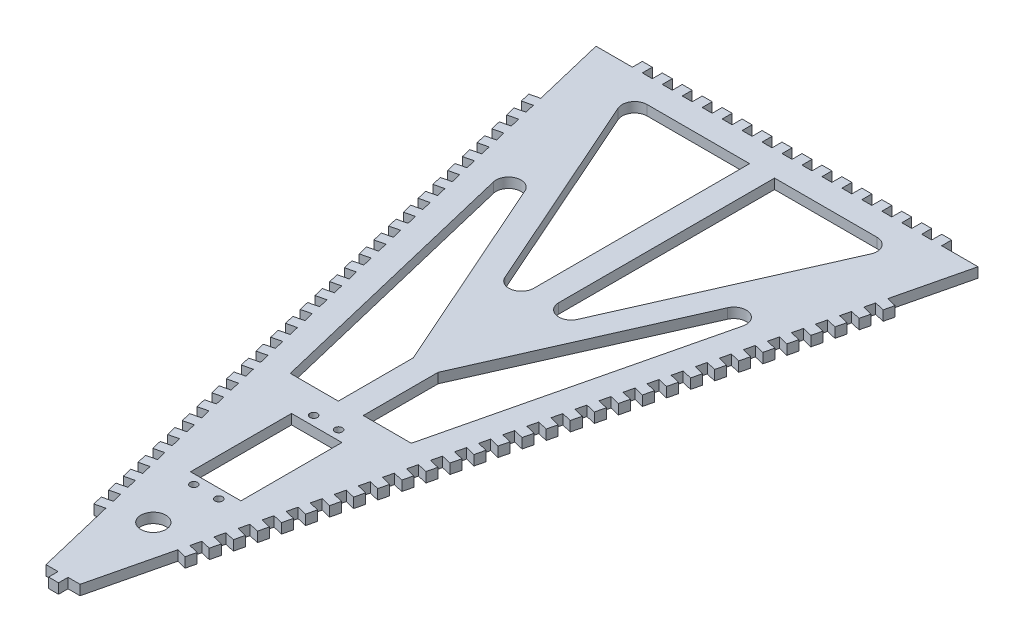
SolidWorks part; units mm, degrees
material "Cedar"
ref_plane "Front Plane" through (0, 0, 0) normal (0, 0, 1) x (1, 0, 0)
ref_plane "Top Plane" through (0, 0, 0) normal (0, 1, 0) x (1, 0, 0)
ref_plane "Right Plane" through (0, 0, 0) normal (1, 0, 0) x (0, 0, -1)
sketch "Sketch1" plane through (0, 0, 0) normal (0, 1, 0) x (1, 0, 0)
  line L0 (-76.56, 0) -> (76.56, 0)
  line L1 (76.56, 0) -> (6.83, -290.231)
  line L2 (6.83, -290.231) -> (-6.83, -290.231)
  line L3 (-6.83, -290.231) -> (-76.56, 0)
  line L4 (0, -290.231) -> (0, 0) construction
  dimension "D1" = 153.12
  dimension "D2" = 13.66
  dimension "D3" = 298.49
extrude "Boss-Extrude1" add sketch "Sketch1" against normal blind 4
sketch "Sketch2" plane through (0, 0, 0) normal (0, 1, 0) x (1, 0, 0)
  line L0 (0, 0) -> (0, -290.231) construction
  line L1 (-6.83, -290.231) -> (6.83, -290.231) construction
  line L2 (-69.5517, -29.1699) -> (-73.441, -30.1044)
  line L3 (-76.56, 0) -> (-6.83, -290.231) construction
  line L4 (-73.441, -30.1044) -> (-72.5066, -33.9937)
  line L5 (-72.5066, -33.9937) -> (-68.6173, -33.0592)
  line L6 (-68.6173, -33.0592) -> (-69.5517, -29.1699)
  line L7 (-67.6829, -36.9486) -> (-71.5722, -37.883)
  line L8 (-71.5722, -37.883) -> (-70.6377, -41.7723)
  line L9 (-70.6377, -41.7723) -> (-66.7484, -40.8379)
  line L10 (-66.7484, -40.8379) -> (-67.6829, -36.9486)
  line L11 (-65.814, -44.7272) -> (-69.7033, -45.6616)
  line L12 (-69.7033, -45.6616) -> (-68.7689, -49.551)
  line L13 (-68.7689, -49.551) -> (-64.8795, -48.6165)
  line L14 (-64.8795, -48.6165) -> (-65.814, -44.7272)
  line L15 (-63.9451, -52.5059) -> (-67.8344, -53.4403)
  line L16 (-67.8344, -53.4403) -> (-66.9, -57.3296)
  line L17 (-66.9, -57.3296) -> (-63.0107, -56.3952)
  line L18 (-63.0107, -56.3952) -> (-63.9451, -52.5059)
  line L19 (-62.0762, -60.2845) -> (-65.9656, -61.2189)
  line L20 (-65.9656, -61.2189) -> (-65.0311, -65.1083)
  line L21 (-65.0311, -65.1083) -> (-61.1418, -64.1738)
  line L22 (-61.1418, -64.1738) -> (-62.0762, -60.2845)
  line L23 (-60.2074, -68.0631) -> (-64.0967, -68.9976)
  line L24 (-64.0967, -68.9976) -> (-63.1622, -72.8869)
  line L25 (-63.1622, -72.8869) -> (-59.2729, -71.9525)
  line L26 (-59.2729, -71.9525) -> (-60.2074, -68.0631)
  line L27 (-58.3385, -75.8418) -> (-62.2278, -76.7762)
  line L28 (-62.2278, -76.7762) -> (-61.2934, -80.6655)
  line L29 (-61.2934, -80.6655) -> (-57.404, -79.7311)
  line L30 (-57.404, -79.7311) -> (-58.3385, -75.8418)
  line L31 (-56.4696, -83.6204) -> (-60.3589, -84.5549)
  line L32 (-60.3589, -84.5549) -> (-59.4245, -88.4442)
  line L33 (-59.4245, -88.4442) -> (-55.5352, -87.5098)
  line L34 (-55.5352, -87.5098) -> (-56.4696, -83.6204)
  line L35 (-54.6007, -91.3991) -> (-58.4901, -92.3335)
  line L36 (-58.4901, -92.3335) -> (-57.5556, -96.2228)
  line L37 (-57.5556, -96.2228) -> (-53.6663, -95.2884)
  line L38 (-53.6663, -95.2884) -> (-54.6007, -91.3991)
  line L39 (-52.7319, -99.1777) -> (-56.6212, -100.1122)
  line L40 (-56.6212, -100.1122) -> (-55.6868, -104.0015)
  line L41 (-55.6868, -104.0015) -> (-51.7974, -103.067)
  line L42 (-51.7974, -103.067) -> (-52.7319, -99.1777)
  line L43 (-50.863, -106.9564) -> (-54.7523, -107.8908)
  line L44 (-54.7523, -107.8908) -> (-53.8179, -111.7801)
  line L45 (-53.8179, -111.7801) -> (-49.9286, -110.8457)
  line L46 (-49.9286, -110.8457) -> (-50.863, -106.9564)
  line L47 (-48.9941, -114.735) -> (-52.8834, -115.6694)
  line L48 (-52.8834, -115.6694) -> (-51.949, -119.5588)
  line L49 (-51.949, -119.5588) -> (-48.0597, -118.6243)
  line L50 (-48.0597, -118.6243) -> (-48.9941, -114.735)
  line L51 (-47.1252, -122.5137) -> (-51.0146, -123.4481)
  line L52 (-51.0146, -123.4481) -> (-50.0801, -127.3374)
  line L53 (-50.0801, -127.3374) -> (-46.1908, -126.403)
  line L54 (-46.1908, -126.403) -> (-47.1252, -122.5137)
  line L55 (-45.2564, -130.2923) -> (-49.1457, -131.2267)
  line L56 (-49.1457, -131.2267) -> (-48.2113, -135.1161)
  line L57 (-48.2113, -135.1161) -> (-44.3219, -134.1816)
  line L58 (-44.3219, -134.1816) -> (-45.2564, -130.2923)
  line L59 (-43.3875, -138.0709) -> (-47.2768, -139.0054)
  line L60 (-47.2768, -139.0054) -> (-46.3424, -142.8947)
  line L61 (-46.3424, -142.8947) -> (-42.4531, -141.9603)
  line L62 (-42.4531, -141.9603) -> (-43.3875, -138.0709)
  line L63 (-41.5186, -145.8496) -> (-45.4079, -146.784)
  line L64 (-45.4079, -146.784) -> (-44.4735, -150.6733)
  line L65 (-44.4735, -150.6733) -> (-40.5842, -149.7389)
  line L66 (-40.5842, -149.7389) -> (-41.5186, -145.8496)
  line L67 (-39.6498, -153.6282) -> (-43.5391, -154.5627)
  line L68 (-43.5391, -154.5627) -> (-42.6046, -158.452)
  line L69 (-42.6046, -158.452) -> (-38.7153, -157.5176)
  line L70 (-38.7153, -157.5176) -> (-39.6498, -153.6282)
  line L71 (-37.7809, -161.4069) -> (-41.6702, -162.3413)
  line L72 (-41.6702, -162.3413) -> (-40.7358, -166.2306)
  line L73 (-40.7358, -166.2306) -> (-36.8464, -165.2962)
  line L74 (-36.8464, -165.2962) -> (-37.7809, -161.4069)
  line L75 (-35.912, -169.1855) -> (-39.8013, -170.12)
  line L76 (-39.8013, -170.12) -> (-38.8669, -174.0093)
  line L77 (-38.8669, -174.0093) -> (-34.9776, -173.0748)
  line L78 (-34.9776, -173.0748) -> (-35.912, -169.1855)
  line L79 (-34.0431, -176.9642) -> (-37.9325, -177.8986)
  line L80 (-37.9325, -177.8986) -> (-36.998, -181.7879)
  line L81 (-36.998, -181.7879) -> (-33.1087, -180.8535)
  line L82 (-33.1087, -180.8535) -> (-34.0431, -176.9642)
  line L83 (-32.1743, -184.7428) -> (-36.0636, -185.6772)
  line L84 (-36.0636, -185.6772) -> (-35.1291, -189.5666)
  line L85 (-35.1291, -189.5666) -> (-31.2398, -188.6321)
  line L86 (-31.2398, -188.6321) -> (-32.1743, -184.7428)
  line L87 (-30.3054, -192.5215) -> (-34.1947, -193.4559)
  line L88 (-34.1947, -193.4559) -> (-33.2603, -197.3452)
  line L89 (-33.2603, -197.3452) -> (-29.3709, -196.4108)
  line L90 (-29.3709, -196.4108) -> (-30.3054, -192.5215)
  line L91 (-28.4365, -200.3001) -> (-32.3258, -201.2345)
  line L92 (-32.3258, -201.2345) -> (-31.3914, -205.1239)
  line L93 (-31.3914, -205.1239) -> (-27.5021, -204.1894)
  line L94 (-27.5021, -204.1894) -> (-28.4365, -200.3001)
  line L95 (-26.5676, -208.0787) -> (-30.457, -209.0132)
  line L96 (-30.457, -209.0132) -> (-29.5225, -212.9025)
  line L97 (-29.5225, -212.9025) -> (-25.6332, -211.9681)
  line L98 (-25.6332, -211.9681) -> (-26.5676, -208.0787)
  line L99 (-24.6988, -215.8574) -> (-28.5881, -216.7918)
  line L100 (-28.5881, -216.7918) -> (-27.6537, -220.6811)
  line L101 (-27.6537, -220.6811) -> (-23.7643, -219.7467)
  line L102 (-23.7643, -219.7467) -> (-24.6988, -215.8574)
  line L103 (-22.8299, -223.636) -> (-26.7192, -224.5705)
  line L104 (-26.7192, -224.5705) -> (-25.7848, -228.4598)
  line L105 (-25.7848, -228.4598) -> (-21.8955, -227.5254)
  line L106 (-21.8955, -227.5254) -> (-22.8299, -223.636)
  line L107 (-20.961, -231.4147) -> (-24.8503, -232.3491)
  line L108 (-24.8503, -232.3491) -> (-23.9159, -236.2384)
  line L109 (-23.9159, -236.2384) -> (-20.0266, -235.304)
  line L110 (-20.0266, -235.304) -> (-20.961, -231.4147)
  line L111 (-19.0921, -239.1933) -> (-22.9815, -240.1278)
  line L112 (-22.9815, -240.1278) -> (-22.047, -244.0171)
  line L113 (-22.047, -244.0171) -> (-18.1577, -243.0826)
  line L114 (-18.1577, -243.0826) -> (-19.0921, -239.1933)
  line L115 (-17.2233, -246.972) -> (-21.1126, -247.9064)
  line L116 (-21.1126, -247.9064) -> (-20.1782, -251.7957)
  line L117 (-20.1782, -251.7957) -> (-16.2888, -250.8613)
  line L118 (-16.2888, -250.8613) -> (-17.2233, -246.972)
  line L119 (-15.3544, -254.7506) -> (-19.2437, -255.685)
  line L120 (-19.2437, -255.685) -> (-18.3093, -259.5744)
  line L121 (-18.3093, -259.5744) -> (-14.42, -258.6399)
  line L122 (-14.42, -258.6399) -> (-15.3544, -254.7506)
  line L123 (14.42, -258.6399) -> (15.3544, -254.7506)
  line L124 (18.3093, -259.5744) -> (14.42, -258.6399)
  line L125 (19.2437, -255.685) -> (18.3093, -259.5744)
  line L126 (15.3544, -254.7506) -> (19.2437, -255.685)
  line L127 (16.2888, -250.8613) -> (17.2233, -246.972)
  line L128 (20.1782, -251.7957) -> (16.2888, -250.8613)
  line L129 (21.1126, -247.9064) -> (20.1782, -251.7957)
  line L130 (17.2233, -246.972) -> (21.1126, -247.9064)
  line L131 (18.1577, -243.0826) -> (19.0921, -239.1933)
  line L132 (22.047, -244.0171) -> (18.1577, -243.0826)
  line L133 (22.9815, -240.1278) -> (22.047, -244.0171)
  line L134 (19.0921, -239.1933) -> (22.9815, -240.1278)
  line L135 (20.0266, -235.304) -> (20.961, -231.4147)
  line L136 (23.9159, -236.2384) -> (20.0266, -235.304)
  line L137 (24.8503, -232.3491) -> (23.9159, -236.2384)
  line L138 (20.961, -231.4147) -> (24.8503, -232.3491)
  line L139 (21.8955, -227.5254) -> (22.8299, -223.636)
  line L140 (25.7848, -228.4598) -> (21.8955, -227.5254)
  line L141 (26.7192, -224.5705) -> (25.7848, -228.4598)
  line L142 (22.8299, -223.636) -> (26.7192, -224.5705)
  line L143 (23.7643, -219.7467) -> (24.6988, -215.8574)
  line L144 (27.6537, -220.6811) -> (23.7643, -219.7467)
  line L145 (28.5881, -216.7918) -> (27.6537, -220.6811)
  line L146 (24.6988, -215.8574) -> (28.5881, -216.7918)
  line L147 (25.6332, -211.9681) -> (26.5676, -208.0787)
  line L148 (29.5225, -212.9025) -> (25.6332, -211.9681)
  line L149 (30.457, -209.0132) -> (29.5225, -212.9025)
  line L150 (26.5676, -208.0787) -> (30.457, -209.0132)
  line L151 (27.5021, -204.1894) -> (28.4365, -200.3001)
  line L152 (31.3914, -205.1239) -> (27.5021, -204.1894)
  line L153 (32.3258, -201.2345) -> (31.3914, -205.1239)
  line L154 (28.4365, -200.3001) -> (32.3258, -201.2345)
  line L155 (29.3709, -196.4108) -> (30.3054, -192.5215)
  line L156 (33.2603, -197.3452) -> (29.3709, -196.4108)
  line L157 (34.1947, -193.4559) -> (33.2603, -197.3452)
  line L158 (30.3054, -192.5215) -> (34.1947, -193.4559)
  line L159 (31.2398, -188.6321) -> (32.1743, -184.7428)
  line L160 (35.1291, -189.5666) -> (31.2398, -188.6321)
  line L161 (36.0636, -185.6772) -> (35.1291, -189.5666)
  line L162 (32.1743, -184.7428) -> (36.0636, -185.6772)
  line L163 (33.1087, -180.8535) -> (34.0431, -176.9642)
  line L164 (36.998, -181.7879) -> (33.1087, -180.8535)
  line L165 (37.9325, -177.8986) -> (36.998, -181.7879)
  line L166 (34.0431, -176.9642) -> (37.9325, -177.8986)
  line L167 (34.9776, -173.0748) -> (35.912, -169.1855)
  line L168 (38.8669, -174.0093) -> (34.9776, -173.0748)
  line L169 (39.8013, -170.12) -> (38.8669, -174.0093)
  line L170 (35.912, -169.1855) -> (39.8013, -170.12)
  line L171 (36.8464, -165.2962) -> (37.7809, -161.4069)
  line L172 (40.7358, -166.2306) -> (36.8464, -165.2962)
  line L173 (41.6702, -162.3413) -> (40.7358, -166.2306)
  line L174 (37.7809, -161.4069) -> (41.6702, -162.3413)
  line L175 (38.7153, -157.5176) -> (39.6498, -153.6282)
  line L176 (42.6046, -158.452) -> (38.7153, -157.5176)
  line L177 (43.5391, -154.5627) -> (42.6046, -158.452)
  line L178 (39.6498, -153.6282) -> (43.5391, -154.5627)
  line L179 (40.5842, -149.7389) -> (41.5186, -145.8496)
  line L180 (44.4735, -150.6733) -> (40.5842, -149.7389)
  line L181 (45.4079, -146.784) -> (44.4735, -150.6733)
  line L182 (41.5186, -145.8496) -> (45.4079, -146.784)
  line L183 (42.4531, -141.9603) -> (43.3875, -138.0709)
  line L184 (46.3424, -142.8947) -> (42.4531, -141.9603)
  line L185 (47.2768, -139.0054) -> (46.3424, -142.8947)
  line L186 (43.3875, -138.0709) -> (47.2768, -139.0054)
  line L187 (44.3219, -134.1816) -> (45.2564, -130.2923)
  line L188 (48.2113, -135.1161) -> (44.3219, -134.1816)
  line L189 (49.1457, -131.2267) -> (48.2113, -135.1161)
  line L190 (45.2564, -130.2923) -> (49.1457, -131.2267)
  line L191 (46.1908, -126.403) -> (47.1252, -122.5137)
  line L192 (50.0801, -127.3374) -> (46.1908, -126.403)
  line L193 (51.0146, -123.4481) -> (50.0801, -127.3374)
  line L194 (47.1252, -122.5137) -> (51.0146, -123.4481)
  line L195 (48.0597, -118.6243) -> (48.9941, -114.735)
  line L196 (51.949, -119.5588) -> (48.0597, -118.6243)
  line L197 (52.8834, -115.6694) -> (51.949, -119.5588)
  line L198 (48.9941, -114.735) -> (52.8834, -115.6694)
  line L199 (49.9286, -110.8457) -> (50.863, -106.9564)
  line L200 (53.8179, -111.7801) -> (49.9286, -110.8457)
  line L201 (54.7523, -107.8908) -> (53.8179, -111.7801)
  line L202 (50.863, -106.9564) -> (54.7523, -107.8908)
  line L203 (51.7974, -103.067) -> (52.7319, -99.1777)
  line L204 (55.6868, -104.0015) -> (51.7974, -103.067)
  line L205 (56.6212, -100.1122) -> (55.6868, -104.0015)
  line L206 (52.7319, -99.1777) -> (56.6212, -100.1122)
  line L207 (53.6663, -95.2884) -> (54.6007, -91.3991)
  line L208 (57.5556, -96.2228) -> (53.6663, -95.2884)
  line L209 (58.4901, -92.3335) -> (57.5556, -96.2228)
  line L210 (54.6007, -91.3991) -> (58.4901, -92.3335)
  line L211 (55.5352, -87.5098) -> (56.4696, -83.6204)
  line L212 (59.4245, -88.4442) -> (55.5352, -87.5098)
  line L213 (60.3589, -84.5549) -> (59.4245, -88.4442)
  line L214 (56.4696, -83.6204) -> (60.3589, -84.5549)
  line L215 (57.404, -79.7311) -> (58.3385, -75.8418)
  line L216 (61.2934, -80.6655) -> (57.404, -79.7311)
  line L217 (62.2278, -76.7762) -> (61.2934, -80.6655)
  line L218 (58.3385, -75.8418) -> (62.2278, -76.7762)
  line L219 (59.2729, -71.9525) -> (60.2074, -68.0631)
  line L220 (63.1622, -72.8869) -> (59.2729, -71.9525)
  line L221 (64.0967, -68.9976) -> (63.1622, -72.8869)
  line L222 (60.2074, -68.0631) -> (64.0967, -68.9976)
  line L223 (61.1418, -64.1738) -> (62.0762, -60.2845)
  line L224 (65.0311, -65.1083) -> (61.1418, -64.1738)
  line L225 (65.9656, -61.2189) -> (65.0311, -65.1083)
  line L226 (62.0762, -60.2845) -> (65.9656, -61.2189)
  line L227 (63.0107, -56.3952) -> (63.9451, -52.5059)
  line L228 (66.9, -57.3296) -> (63.0107, -56.3952)
  line L229 (67.8344, -53.4403) -> (66.9, -57.3296)
  line L230 (63.9451, -52.5059) -> (67.8344, -53.4403)
  line L231 (64.8795, -48.6165) -> (65.814, -44.7272)
  line L232 (68.7689, -49.551) -> (64.8795, -48.6165)
  line L233 (69.7033, -45.6616) -> (68.7689, -49.551)
  line L234 (65.814, -44.7272) -> (69.7033, -45.6616)
  line L235 (66.7484, -40.8379) -> (67.6829, -36.9486)
  line L236 (70.6377, -41.7723) -> (66.7484, -40.8379)
  line L237 (71.5722, -37.883) -> (70.6377, -41.7723)
  line L238 (67.6829, -36.9486) -> (71.5722, -37.883)
  line L239 (68.6173, -33.0592) -> (69.5517, -29.1699)
  line L240 (72.5066, -33.9937) -> (68.6173, -33.0592)
  line L241 (73.441, -30.1044) -> (72.5066, -33.9937)
  line L242 (69.5517, -29.1699) -> (73.441, -30.1044)
  dimension "D1" = 4
  dimension "D2" = 4
  dimension "D3" = 30
  dimension "D4" = 30
extrude "Boss-Extrude2" add sketch "Sketch2" against normal blind 4
sketch "Sketch3" plane through (0, 0, 0) normal (0, 1, 0) x (1, 0, 0)
  line L0 (0, 0) -> (0, 56.15) construction
  line L1 (76.56, 0) -> (-76.56, 0) construction
  line L2 (-2, 0) -> (-6, 0)
  line L3 (-2, 0) -> (-2, 4)
  line L4 (-2, 4) -> (-6, 4)
  line L5 (-6, 0) -> (-6, 4)
  line L6 (-10, 0) -> (-10, 4)
  line L7 (-10, 4) -> (-14, 4)
  line L8 (-14, 0) -> (-14, 4)
  line L9 (-10, 0) -> (-14, 0)
  line L10 (-18, 0) -> (-18, 4)
  line L11 (-18, 4) -> (-22, 4)
  line L12 (-22, 0) -> (-22, 4)
  line L13 (-18, 0) -> (-22, 0)
  line L14 (-26, 0) -> (-26, 4)
  line L15 (-26, 4) -> (-30, 4)
  line L16 (-30, 0) -> (-30, 4)
  line L17 (-26, 0) -> (-30, 0)
  line L18 (-34, 0) -> (-34, 4)
  line L19 (-34, 4) -> (-38, 4)
  line L20 (-38, 0) -> (-38, 4)
  line L21 (-34, 0) -> (-38, 0)
  line L22 (-42, 0) -> (-42, 4)
  line L23 (-42, 4) -> (-46, 4)
  line L24 (-46, 0) -> (-46, 4)
  line L25 (-42, 0) -> (-46, 0)
  line L26 (-50, 0) -> (-50, 4)
  line L27 (-50, 4) -> (-54, 4)
  line L28 (-54, 0) -> (-54, 4)
  line L29 (-50, 0) -> (-54, 0)
  line L30 (-58, 0) -> (-58, 4)
  line L31 (-58, 4) -> (-62, 4)
  line L32 (-62, 0) -> (-62, 4)
  line L33 (-58, 0) -> (-62, 0)
  line L34 (58, 0) -> (62, 0)
  line L35 (62, 0) -> (62, 4)
  line L36 (58, 4) -> (62, 4)
  line L37 (58, 0) -> (58, 4)
  line L38 (50, 0) -> (54, 0)
  line L39 (54, 0) -> (54, 4)
  line L40 (50, 4) -> (54, 4)
  line L41 (50, 0) -> (50, 4)
  line L42 (42, 0) -> (46, 0)
  line L43 (46, 0) -> (46, 4)
  line L44 (42, 4) -> (46, 4)
  line L45 (42, 0) -> (42, 4)
  line L46 (34, 0) -> (38, 0)
  line L47 (38, 0) -> (38, 4)
  line L48 (34, 4) -> (38, 4)
  line L49 (34, 0) -> (34, 4)
  line L50 (26, 0) -> (30, 0)
  line L51 (30, 0) -> (30, 4)
  line L52 (26, 4) -> (30, 4)
  line L53 (26, 0) -> (26, 4)
  line L54 (18, 0) -> (22, 0)
  line L55 (22, 0) -> (22, 4)
  line L56 (18, 4) -> (22, 4)
  line L57 (18, 0) -> (18, 4)
  line L58 (10, 0) -> (14, 0)
  line L59 (14, 0) -> (14, 4)
  line L60 (10, 4) -> (14, 4)
  line L61 (10, 0) -> (10, 4)
  line L62 (6, 0) -> (6, 4)
  line L63 (2, 4) -> (6, 4)
  line L64 (2, 0) -> (2, 4)
  line L65 (2, 0) -> (6, 0)
  line L67 (-2, -290.0303) -> (2, -290.0303)
  line L68 (-2, -290.0303) -> (-2, -294.0303)
  line L69 (-2, -294.0303) -> (2, -294.0303)
  line L70 (2, -290.0303) -> (2, -294.0303)
  line L71 (0, -290.0303) -> (0, -282.366) construction
  dimension "D1" = 2
  dimension "D2" = 4
  dimension "D3" = 4
  dimension "D5" = 4
  dimension "D6" = 4
  dimension "D4" = 8
extrude "Boss-Extrude3" add sketch "Sketch3" against normal blind 4
sketch "Sketch4" plane through (0, 0, 0) normal (0, 1, 0) x (1, 0, 0)
  line L0 (-46.0754, -10) -> (-5, -10)
  line L1 (-5, -10) -> (-5, -96.5137)
  line L2 (-14.5722, -98.5372) -> (-50.6477, -17.0235)
  line L3 (-40.586, -64.4676) -> (-5, -144.8753)
  line L4 (-5, -144.8753) -> (-5, -174.8753)
  line L5 (-24.2604, -174.8753) -> (-50.0198, -67.6592)
  line L6 (-76.56, 0) -> (-69.5517, -29.1699) construction
  line L7 (-62, 0) -> (-76.56, 0) construction
  line L8 (-50.1287, -18.1961) -> (-59.2732, -22.2432) construction
  line L9 (-54.7009, -20.2197) -> (-62.2686, -3.1202) construction
  line L10 (-62.9005, -14.0471) -> (-58.3283, -12.0235) construction
  line L11 (-58.3283, -12.0235) -> (-53.7561, -10) construction
  line L12 (0, 0) -> (0, -45.6082) construction
  line L13 (58.3283, -12.0235) -> (53.7561, -10) construction
  line L14 (62.9005, -14.0471) -> (58.3283, -12.0235) construction
  line L15 (54.7009, -20.2197) -> (62.2686, -3.1202) construction
  line L16 (50.1287, -18.1961) -> (59.2732, -22.2432) construction
  line L17 (24.2604, -174.8753) -> (50.0198, -67.6592)
  line L18 (5, -144.8753) -> (5, -174.8753)
  line L19 (40.586, -64.4676) -> (5, -144.8753)
  line L20 (14.5722, -98.5372) -> (50.6477, -17.0235)
  line L21 (5, -10) -> (5, -96.5137)
  line L22 (46.0754, -10) -> (5, -10)
  line L24 (-24.2604, -174.8753) -> (-5, -174.8753)
  line L25 (5, -174.8753) -> (24.2604, -174.8753)
  arc A2 (50.0198, -67.6592) -> (40.586, -64.4676) centre (45.1582, -66.4911) ccw
  arc A3 (-46.0754, -10) -> (-50.6477, -17.0235) centre (-46.0754, -15) ccw
  arc A4 (50.6477, -17.0235) -> (46.0754, -10) centre (46.0754, -15) ccw
  arc A5 (-40.586, -64.4676) -> (-50.0198, -67.6592) centre (-45.1582, -66.4911) ccw
  arc A6 (-5, -96.5137) -> (-14.5722, -98.5372) centre (-10, -96.5137) cw
  arc A7 (14.5722, -98.5372) -> (5, -96.5137) centre (10, -96.5137) cw
  point P34 (-5, -255.0413)
  point P37 (5, -255.0413)
  point P52 (-5, -120.166)
  point P55 (5, -120.166)
  dimension "D5" = 30
  dimension "D1" = 10
  dimension "D2" = 10
  dimension "D3" = 10
  dimension "D4" = 5
extrude "Cut-Extrude1" cut sketch "Sketch4" against normal blind 4
sketch "Sketch5" plane through (0, 0, 0) normal (0, 1, 0) x (1, 0, 0)
  line L0 (-2, -294.0303) -> (2, -294.0303) construction
  circle A0 centre (0, -254.0303) radius 5
  point P2 (0, -294.0303)
  dimension "D1" = 10
  dimension "D2" = 40
extrude "Cut-Extrude2" cut sketch "Sketch5" against normal blind 10
sketch "Sketch6" plane through (0, 0, 0) normal (0, 1, 0) x (1, 0, 0)
  line L0 (0, -294.0303) -> (0, -229.0303) construction
  line L1 (-10.1, -188.5303) -> (10.1, -188.5303)
  line L2 (-10.1, -188.5303) -> (-10.1, -229.0303)
  line L3 (-10.1, -229.0303) -> (10.1, -229.0303)
  line L4 (10.1, -188.5303) -> (10.1, -229.0303)
  line L5 (-2, -294.0303) -> (2, -294.0303) construction
  line L6 (-10.1, -208.7803) -> (18.1846, -208.7803) construction
  line L7 (0, -188.5303) -> (0, -180.8076) construction
  line L8 (-5, -180.8076) -> (5, -180.8076) construction
  circle A0 centre (0, -254.0303) radius 5 construction
  circle A1 centre (-5, -184.7803) radius 1.5
  circle A2 centre (5, -184.7803) radius 1.5
  circle A3 centre (5, -232.7803) radius 1.5
  circle A4 centre (-5, -232.7803) radius 1.5
  dimension "D5" = 3
  dimension "D1" = 40.5
  dimension "D2" = 20.2
  dimension "D3" = 25
  dimension "D4" = 24
  dimension "D6" = 10
extrude "Cut-Extrude3" cut sketch "Sketch6" against normal blind 4
